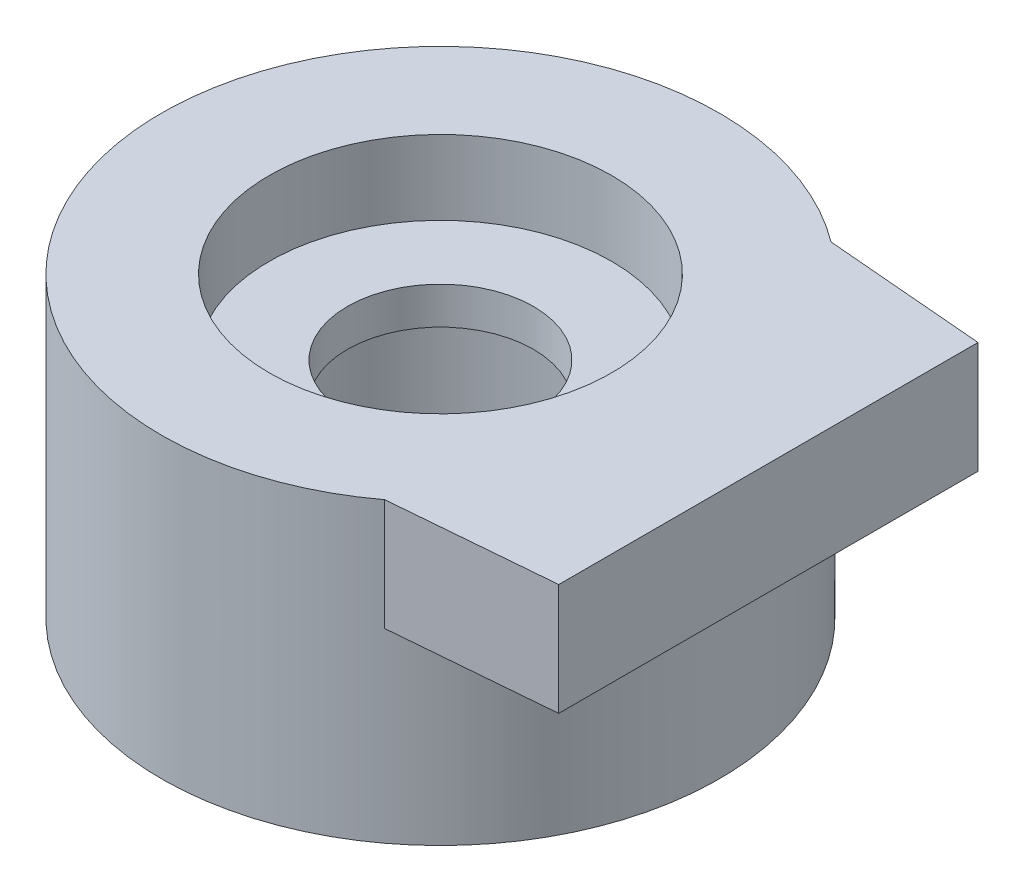
SolidWorks part; units mm, degrees
ref_plane "Front Plane" through (0, 0, 0) normal (0, 0, 1) x (1, 0, 0)
ref_plane "Top Plane" through (0, 0, 0) normal (0, 1, 0) x (1, 0, 0)
ref_plane "Right Plane" through (0, 0, 0) normal (1, 0, 0) x (0, 0, -1)
ref_plane "Plane1" through (0, 4, 0) normal (0, 1, 0) x (1, 0, 0)
sketch "Sketch1" plane through (0, 4, 0) normal (0, 1, 0) x (1, 0, 0)
  line L0 (2.25, -3) -> (4.4078, -2.8177)
  line L1 (4.4078, -2.8177) -> (4.4078, 2.8177)
  line L2 (4.4078, 2.8177) -> (2.25, 3)
  arc A0 (2.25, 3) -> (2.25, -3) centre (0, 0) ccw
extrude "Boss-Extrude1" add sketch "Sketch1" against normal blind 1.5
sketch "Sketch2" plane through (0, 2.5, 0) normal (0, -1, 0) x (1, 0, 0)
  circle A0 centre (0, 0) radius 3.75
extrude "Boss-Extrude2" add sketch "Sketch2" along normal blind 2.5
ref_plane "Plane2" through (0, 0, 0) normal (0, 0, -1) x (-1, 0, 0)
sketch "Sketch3" plane through (0, 0, 0) normal (0, 0, -1) x (-1, 0, 0)
  line L0 (-2.3, 0) -> (0, 0)
  line L1 (0, 0) -> (0, 4)
  line L2 (0, 4) -> (-2.3, 4)
  line L3 (-2.3, 4) -> (-2.3, 3)
  line L4 (-2.3, 3) -> (-1.25, 3)
  line L5 (-1.25, 3) -> (-1.25, 2.5)
  line L6 (-1.25, 2.5) -> (-2.3, 2.5)
  line L7 (-2.3, 2.5) -> (-2.3, 0)
  line L8 (0, 0) -> (0, 4) construction
revolve "Cut-Revolve1" cut sketch "Sketch3" angle 360 about L8
